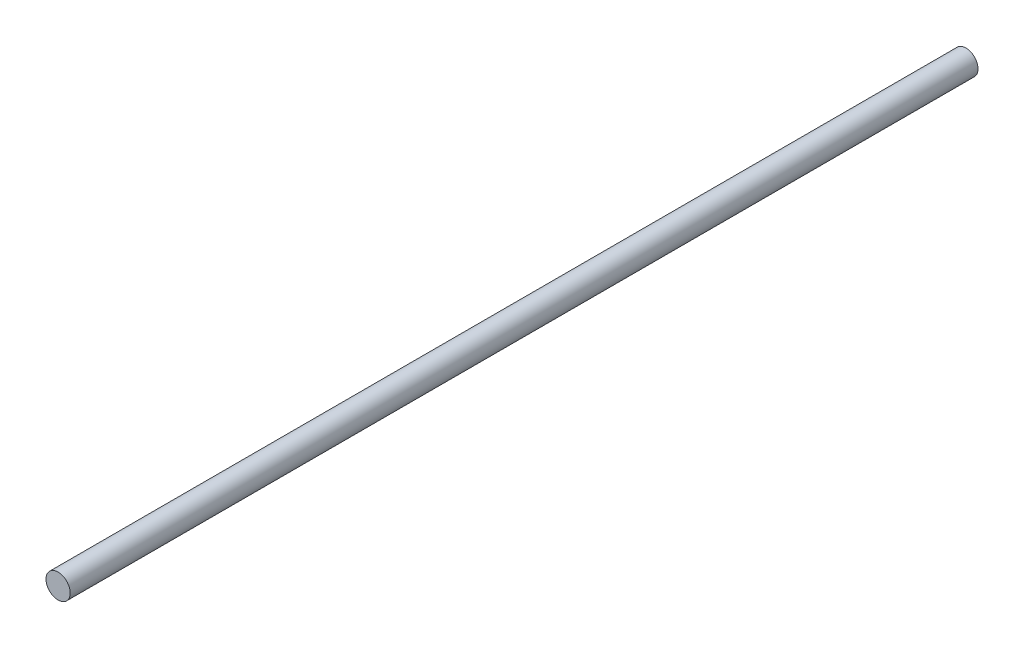
SolidWorks part; units mm, degrees
ref_plane "Front Plane" through (0, 0, 0) normal (0, 0, 1) x (1, 0, 0)
ref_plane "Top Plane" through (0, 0, 0) normal (0, 1, 0) x (1, 0, 0)
ref_plane "Right Plane" through (0, 0, 0) normal (1, 0, 0) x (0, 0, -1)
sketch "Sketch1" plane through (0, 0, 0) normal (0, 0, 1) x (1, 0, 0)
  circle A0 centre (0, 0) radius 2
  dimension "D1" = 4
extrude "Boss-Extrude1" add sketch "Sketch1" along normal blind 100 and the other way blind 50
